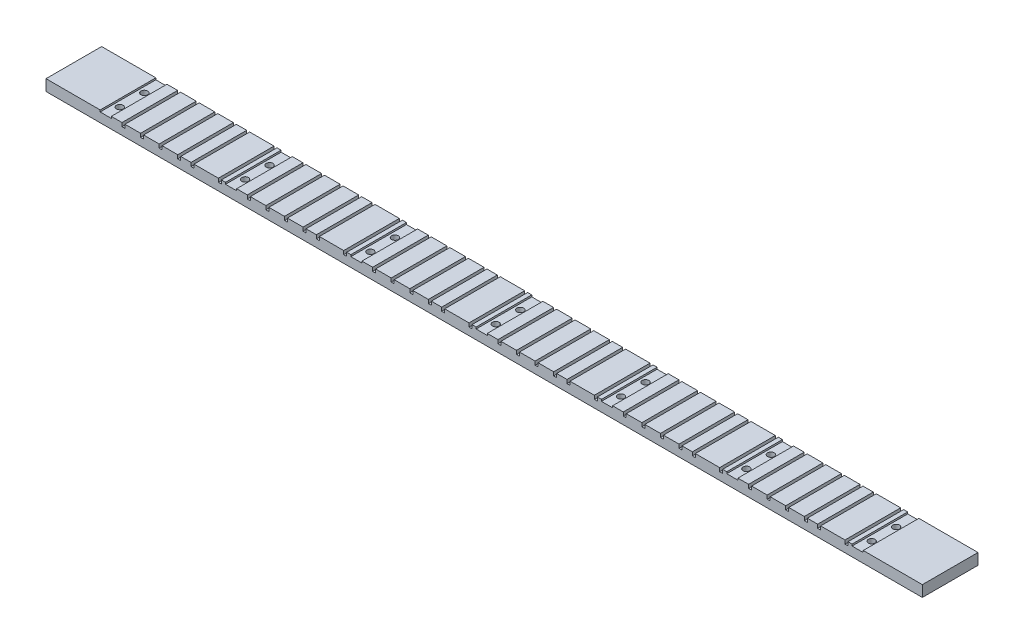
SolidWorks part; units mm, degrees
ref_plane "Front Plane" through (0, 0, 0) normal (0, 0, 1) x (1, 0, 0)
ref_plane "Top Plane" through (0, 0, 0) normal (0, 1, 0) x (1, 0, 0)
ref_plane "Right Plane" through (0, 0, 0) normal (1, 0, 0) x (0, 0, -1)
ref_plane "Plane1" through (0, 2, 0) normal (0, -1, 0) x (-1, 0, 0)
sketch "Sketch1" plane through (0, 2, 0) normal (0, -1, 0) x (-1, 0, 0)
  line L1 (100, 20) -> (-400, 20)
  line L2 (100, 20) -> (100, 51.75)
  line L3 (100, 51.75) -> (-400, 51.75)
  line L4 (-400, 20) -> (-400, 51.75)
extrude "Boss-Extrude1" add sketch "Sketch1" along normal blind 6.35
sketch "Sketch5" plane through (0, 0, -51.75) normal (0, 0, -1) x (-1, 0, 0)
  line L0 (-1.5747, 2.0001) -> (-0.0572, 2.0001)
  line L1 (-1.5747, 3.3668) -> (-1.5747, 2.0001)
  line L2 (61.7105, 3.3668) -> (-1.5747, 3.3668)
  line L3 (61.7105, 2.0001) -> (61.7105, 3.3668)
  line L4 (56.6446, -0.0571) -> (56.6446, 2.0001)
  line L5 (54.9428, 2.0001) -> (54.9428, -0.0571)
  line L6 (46.0446, 2.0001) -> (54.9428, 2.0001)
  line L7 (46.0446, -0.0571) -> (46.0446, 2.0001)
  line L8 (44.3428, -0.0571) -> (46.0446, -0.0571)
  line L9 (44.3428, 2.0001) -> (44.3428, -0.0571)
  line L10 (35.4446, 2.0001) -> (44.3428, 2.0001)
  line L11 (35.4446, -0.0571) -> (35.4446, 2.0001)
  line L12 (33.7428, -0.0571) -> (35.4446, -0.0571)
  line L174 (54.9428, -0.0571) -> (56.6446, -0.0571)
  line L181 (33.7428, 2.0001) -> (33.7428, -0.0571)
  line L182 (24.8446, 2.0001) -> (33.7428, 2.0001)
  line L183 (24.8446, -0.0571) -> (24.8446, 2.0001)
  line L184 (23.1428, -0.0571) -> (24.8446, -0.0571)
  line L185 (23.1428, 2.0001) -> (23.1428, -0.0571)
  line L186 (17.2446, 2.0001) -> (23.1428, 2.0001)
  line L187 (17.2446, -0.0571) -> (17.2446, 2.0001)
  line L188 (15.5428, -0.0571) -> (17.2446, -0.0571)
  line L189 (15.5428, 2.0001) -> (15.5428, -0.0571)
  line L190 (1.6446, 2.0001) -> (15.5428, 2.0001)
  line L191 (1.6446, -0.0571) -> (1.6446, 2.0001)
  line L192 (-0.0572, -0.0571) -> (1.6446, -0.0571)
  line L193 (-0.0572, 2.0001) -> (-0.0572, -0.0571)
  line L194 (-73.0747, 2.0001) -> (-71.5572, 2.0001)
  line L195 (-73.0747, 3.3668) -> (-73.0747, 2.0001)
  line L196 (-9.7895, 3.3668) -> (-73.0747, 3.3668)
  line L197 (-9.7895, 2.0001) -> (-9.7895, 3.3668)
  line L198 (-14.8554, 2.0001) -> (-9.7895, 2.0001)
  line L199 (-14.8554, -0.0571) -> (-14.8554, 2.0001)
  line L200 (-16.5572, -0.0571) -> (-14.8554, -0.0571)
  line L201 (-16.5572, 2.0001) -> (-16.5572, -0.0571)
  line L202 (-25.4554, 2.0001) -> (-16.5572, 2.0001)
  line L203 (-25.4554, -0.0571) -> (-25.4554, 2.0001)
  line L204 (-27.1572, -0.0571) -> (-25.4554, -0.0571)
  line L205 (-27.1572, 2.0001) -> (-27.1572, -0.0571)
  line L206 (-36.0554, 2.0001) -> (-27.1572, 2.0001)
  line L207 (-36.0554, -0.0571) -> (-36.0554, 2.0001)
  line L208 (-37.7572, -0.0571) -> (-36.0554, -0.0571)
  line L209 (-37.7572, 2.0001) -> (-37.7572, -0.0571)
  line L210 (-46.6554, 2.0001) -> (-37.7572, 2.0001)
  line L211 (-46.6554, -0.0571) -> (-46.6554, 2.0001)
  line L212 (-48.3572, -0.0571) -> (-46.6554, -0.0571)
  line L213 (-48.3572, 2.0001) -> (-48.3572, -0.0571)
  line L214 (-54.2554, 2.0001) -> (-48.3572, 2.0001)
  line L215 (-54.2554, -0.0571) -> (-54.2554, 2.0001)
  line L216 (-55.9572, -0.0571) -> (-54.2554, -0.0571)
  line L217 (-55.9572, 2.0001) -> (-55.9572, -0.0571)
  line L218 (-69.8554, 2.0001) -> (-55.9572, 2.0001)
  line L219 (-69.8554, -0.0571) -> (-69.8554, 2.0001)
  line L220 (-71.5572, -0.0571) -> (-69.8554, -0.0571)
  line L221 (-71.5572, 2.0001) -> (-71.5572, -0.0571)
  line L222 (-144.5747, 2.0001) -> (-143.0572, 2.0001)
  line L223 (-144.5747, 3.3668) -> (-144.5747, 2.0001)
  line L224 (-81.2895, 3.3668) -> (-144.5747, 3.3668)
  line L225 (-81.2895, 2.0001) -> (-81.2895, 3.3668)
  line L226 (-86.3554, 2.0001) -> (-81.2895, 2.0001)
  line L227 (-86.3554, -0.0571) -> (-86.3554, 2.0001)
  line L228 (-88.0572, -0.0571) -> (-86.3554, -0.0571)
  line L229 (-88.0572, 2.0001) -> (-88.0572, -0.0571)
  line L230 (-96.9554, 2.0001) -> (-88.0572, 2.0001)
  line L231 (-96.9554, -0.0571) -> (-96.9554, 2.0001)
  line L232 (-98.6572, -0.0571) -> (-96.9554, -0.0571)
  line L233 (-98.6572, 2.0001) -> (-98.6572, -0.0571)
  line L234 (-107.5554, 2.0001) -> (-98.6572, 2.0001)
  line L235 (-107.5554, -0.0571) -> (-107.5554, 2.0001)
  line L236 (-109.2572, -0.0571) -> (-107.5554, -0.0571)
  line L237 (-109.2572, 2.0001) -> (-109.2572, -0.0571)
  line L238 (-118.1554, 2.0001) -> (-109.2572, 2.0001)
  line L239 (-118.1554, -0.0571) -> (-118.1554, 2.0001)
  line L240 (-119.8572, -0.0571) -> (-118.1554, -0.0571)
  line L241 (-119.8572, 2.0001) -> (-119.8572, -0.0571)
  line L242 (-125.7554, 2.0001) -> (-119.8572, 2.0001)
  line L243 (-125.7554, -0.0571) -> (-125.7554, 2.0001)
  line L244 (-127.4572, -0.0571) -> (-125.7554, -0.0571)
  line L245 (-127.4572, 2.0001) -> (-127.4572, -0.0571)
  line L246 (-141.3554, 2.0001) -> (-127.4572, 2.0001)
  line L247 (-141.3554, -0.0571) -> (-141.3554, 2.0001)
  line L248 (-143.0572, -0.0571) -> (-141.3554, -0.0571)
  line L249 (-143.0572, 2.0001) -> (-143.0572, -0.0571)
  line L250 (-216.0747, 2.0001) -> (-214.5572, 2.0001)
  line L251 (-216.0747, 3.3668) -> (-216.0747, 2.0001)
  line L252 (-152.7895, 3.3668) -> (-216.0747, 3.3668)
  line L253 (-152.7895, 2.0001) -> (-152.7895, 3.3668)
  line L254 (-157.8554, 2.0001) -> (-152.7895, 2.0001)
  line L255 (-157.8554, -0.0571) -> (-157.8554, 2.0001)
  line L256 (-159.5572, -0.0571) -> (-157.8554, -0.0571)
  line L257 (-159.5572, 2.0001) -> (-159.5572, -0.0571)
  line L258 (-168.4554, 2.0001) -> (-159.5572, 2.0001)
  line L259 (-168.4554, -0.0571) -> (-168.4554, 2.0001)
  line L260 (-170.1572, -0.0571) -> (-168.4554, -0.0571)
  line L261 (-170.1572, 2.0001) -> (-170.1572, -0.0571)
  line L262 (-179.0554, 2.0001) -> (-170.1572, 2.0001)
  line L263 (-179.0554, -0.0571) -> (-179.0554, 2.0001)
  line L264 (-180.7572, -0.0571) -> (-179.0554, -0.0571)
  line L265 (-180.7572, 2.0001) -> (-180.7572, -0.0571)
  line L266 (-189.6554, 2.0001) -> (-180.7572, 2.0001)
  line L267 (-189.6554, -0.0571) -> (-189.6554, 2.0001)
  line L268 (-191.3572, -0.0571) -> (-189.6554, -0.0571)
  line L269 (-191.3572, 2.0001) -> (-191.3572, -0.0571)
  line L270 (-197.2554, 2.0001) -> (-191.3572, 2.0001)
  line L271 (-197.2554, -0.0571) -> (-197.2554, 2.0001)
  line L272 (-198.9572, -0.0571) -> (-197.2554, -0.0571)
  line L273 (-198.9572, 2.0001) -> (-198.9572, -0.0571)
  line L274 (-212.8554, 2.0001) -> (-198.9572, 2.0001)
  line L275 (-212.8554, -0.0571) -> (-212.8554, 2.0001)
  line L276 (-214.5572, -0.0571) -> (-212.8554, -0.0571)
  line L277 (-214.5572, 2.0001) -> (-214.5572, -0.0571)
  line L278 (-287.5747, 2.0001) -> (-286.0572, 2.0001)
  line L279 (-287.5747, 3.3668) -> (-287.5747, 2.0001)
  line L280 (-224.2895, 3.3668) -> (-287.5747, 3.3668)
  line L281 (-224.2895, 2.0001) -> (-224.2895, 3.3668)
  line L282 (-229.3554, 2.0001) -> (-224.2895, 2.0001)
  line L283 (-229.3554, -0.0571) -> (-229.3554, 2.0001)
  line L284 (-231.0572, -0.0571) -> (-229.3554, -0.0571)
  line L285 (-231.0572, 2.0001) -> (-231.0572, -0.0571)
  line L286 (-239.9554, 2.0001) -> (-231.0572, 2.0001)
  line L287 (-239.9554, -0.0571) -> (-239.9554, 2.0001)
  line L288 (-241.6572, -0.0571) -> (-239.9554, -0.0571)
  line L289 (-241.6572, 2.0001) -> (-241.6572, -0.0571)
  line L290 (-250.5554, 2.0001) -> (-241.6572, 2.0001)
  line L291 (-250.5554, -0.0571) -> (-250.5554, 2.0001)
  line L292 (-252.2572, -0.0571) -> (-250.5554, -0.0571)
  line L293 (-252.2572, 2.0001) -> (-252.2572, -0.0571)
  line L294 (-261.1554, 2.0001) -> (-252.2572, 2.0001)
  line L295 (-261.1554, -0.0571) -> (-261.1554, 2.0001)
  line L296 (-262.8572, -0.0571) -> (-261.1554, -0.0571)
  line L297 (-262.8572, 2.0001) -> (-262.8572, -0.0571)
  line L298 (-268.7554, 2.0001) -> (-262.8572, 2.0001)
  line L299 (-268.7554, -0.0571) -> (-268.7554, 2.0001)
  line L300 (-270.4572, -0.0571) -> (-268.7554, -0.0571)
  line L301 (-270.4572, 2.0001) -> (-270.4572, -0.0571)
  line L302 (-284.3554, 2.0001) -> (-270.4572, 2.0001)
  line L303 (-284.3554, -0.0571) -> (-284.3554, 2.0001)
  line L304 (-286.0572, -0.0571) -> (-284.3554, -0.0571)
  line L305 (-286.0572, 2.0001) -> (-286.0572, -0.0571)
  line L306 (-359.0747, 2.0001) -> (-357.5572, 2.0001)
  line L307 (-359.0747, 3.3668) -> (-359.0747, 2.0001)
  line L308 (-295.7895, 3.3668) -> (-359.0747, 3.3668)
  line L309 (-295.7895, 2.0001) -> (-295.7895, 3.3668)
  line L310 (-300.8554, 2.0001) -> (-295.7895, 2.0001)
  line L311 (-300.8554, -0.0571) -> (-300.8554, 2.0001)
  line L312 (-302.5572, -0.0571) -> (-300.8554, -0.0571)
  line L313 (-302.5572, 2.0001) -> (-302.5572, -0.0571)
  line L314 (-311.4554, 2.0001) -> (-302.5572, 2.0001)
  line L315 (-311.4554, -0.0571) -> (-311.4554, 2.0001)
  line L316 (-313.1572, -0.0571) -> (-311.4554, -0.0571)
  line L317 (-313.1572, 2.0001) -> (-313.1572, -0.0571)
  line L318 (-322.0554, 2.0001) -> (-313.1572, 2.0001)
  line L319 (-322.0554, -0.0571) -> (-322.0554, 2.0001)
  line L320 (-323.7572, -0.0571) -> (-322.0554, -0.0571)
  line L321 (-323.7572, 2.0001) -> (-323.7572, -0.0571)
  line L322 (-332.6554, 2.0001) -> (-323.7572, 2.0001)
  line L323 (-332.6554, -0.0571) -> (-332.6554, 2.0001)
  line L324 (-334.3572, -0.0571) -> (-332.6554, -0.0571)
  line L325 (-334.3572, 2.0001) -> (-334.3572, -0.0571)
  line L326 (-340.2554, 2.0001) -> (-334.3572, 2.0001)
  line L327 (-340.2554, -0.0571) -> (-340.2554, 2.0001)
  line L328 (-341.9572, -0.0571) -> (-340.2554, -0.0571)
  line L329 (-341.9572, 2.0001) -> (-341.9572, -0.0571)
  line L330 (-355.8554, 2.0001) -> (-341.9572, 2.0001)
  line L331 (-355.8554, -0.0571) -> (-355.8554, 2.0001)
  line L332 (-357.5572, -0.0571) -> (-355.8554, -0.0571)
  line L333 (-357.5572, 2.0001) -> (-357.5572, -0.0571)
  line L334 (56.6446, 2.0001) -> (61.7105, 2.0001)
extrude "Cut-Extrude2" cut sketch "Sketch5" against normal through all
sketch "Sketch7" plane through (0, 0, -20) normal (0, 0, 1) x (1, 0, 0)
  line L0 (-71.12, 3.6453) -> (-71.12, 2)
  line L2 (-71.12, 2) -> (-69.0919, 2)
  line L3 (-69.0919, 2) -> (-69.0919, 1)
  line L4 (-69.0919, 1) -> (-62.7419, 1)
  line L5 (-62.7419, 1) -> (-62.7419, 2)
  line L6 (-62.7419, 2) -> (-60.964, 2)
  line L7 (-60.964, 2) -> (-60.964, 3.6453)
  line L8 (-71.12, 3.6453) -> (-60.964, 3.6453)
  line L9 (0.38, 3.6453) -> (0.38, 2)
  line L10 (0.38, 2) -> (2.4081, 2)
  line L11 (2.4081, 2) -> (2.4081, 1)
  line L12 (2.4081, 1) -> (8.7581, 1)
  line L13 (8.7581, 1) -> (8.7581, 2)
  line L14 (8.7581, 2) -> (10.536, 2)
  line L15 (10.536, 2) -> (10.536, 3.6453)
  line L16 (0.38, 3.6453) -> (10.536, 3.6453)
  line L17 (71.88, 3.6453) -> (71.88, 2)
  line L18 (71.88, 2) -> (73.9081, 2)
  line L19 (73.9081, 2) -> (73.9081, 1)
  line L20 (73.9081, 1) -> (80.2581, 1)
  line L21 (80.2581, 1) -> (80.2581, 2)
  line L22 (80.2581, 2) -> (82.036, 2)
  line L23 (82.036, 2) -> (82.036, 3.6453)
  line L24 (71.88, 3.6453) -> (82.036, 3.6453)
  line L25 (143.38, 3.6453) -> (143.38, 2)
  line L26 (143.38, 2) -> (145.4081, 2)
  line L27 (145.4081, 2) -> (145.4081, 1)
  line L28 (145.4081, 1) -> (151.7581, 1)
  line L29 (151.7581, 1) -> (151.7581, 2)
  line L30 (151.7581, 2) -> (153.536, 2)
  line L31 (153.536, 2) -> (153.536, 3.6453)
  line L32 (143.38, 3.6453) -> (153.536, 3.6453)
  line L33 (214.88, 3.6453) -> (214.88, 2)
  line L34 (214.88, 2) -> (216.9081, 2)
  line L35 (216.9081, 2) -> (216.9081, 1)
  line L36 (216.9081, 1) -> (223.2581, 1)
  line L37 (223.2581, 1) -> (223.2581, 2)
  line L38 (223.2581, 2) -> (225.036, 2)
  line L39 (225.036, 2) -> (225.036, 3.6453)
  line L40 (214.88, 3.6453) -> (225.036, 3.6453)
  line L41 (286.38, 3.6453) -> (286.38, 2)
  line L42 (286.38, 2) -> (288.4081, 2)
  line L43 (288.4081, 2) -> (288.4081, 1)
  line L44 (288.4081, 1) -> (294.7581, 1)
  line L45 (294.7581, 1) -> (294.7581, 2)
  line L46 (294.7581, 2) -> (296.536, 2)
  line L47 (296.536, 2) -> (296.536, 3.6453)
  line L48 (286.38, 3.6453) -> (296.536, 3.6453)
  line L49 (357.88, 3.6453) -> (357.88, 2)
  line L50 (357.88, 2) -> (359.9081, 2)
  line L51 (359.9081, 2) -> (359.9081, 1)
  line L52 (359.9081, 1) -> (366.2581, 1)
  line L53 (366.2581, 1) -> (366.2581, 2)
  line L54 (366.2581, 2) -> (368.036, 2)
  line L55 (368.036, 2) -> (368.036, 3.6453)
  line L56 (357.88, 3.6453) -> (368.036, 3.6453)
  dimension "D1" = 7
extrude "Cut-Extrude4" cut sketch "Sketch7" against normal through all
sketch "Sketch6" plane through (0, 1, 0) normal (0, -1, 0) x (1, 0, 0)
  line L0 (-65.9169, -20) -> (-65.9169, -49.7477) construction
  line L1 (400, -20) -> (-100, -20) construction
  line L2 (-65.9169, -24.3797) -> (-62.7419, -24.3797) construction
  line L3 (-65.9169, -47.1776) -> (-69.0919, -47.1776) construction
  line L4 (-62.7419, -51.75) -> (-62.7419, -20) construction
  line L5 (-69.0919, -51.75) -> (-69.0919, -20) construction
  circle A0 centre (-65.9169, -42) radius 1.8987
  circle A1 centre (-65.9169, -28) radius 1.8987
  circle A5 centre (5.5831, -42) radius 1.8987
  circle A6 centre (5.5831, -28) radius 1.8987
  circle A7 centre (77.0831, -42) radius 1.8987
  circle A8 centre (77.0831, -28) radius 1.8987
  circle A9 centre (148.5831, -42) radius 1.8987
  circle A10 centre (148.5831, -28) radius 1.8987
  circle A11 centre (220.0831, -42) radius 1.8987
  circle A12 centre (220.0831, -28) radius 1.8987
  circle A13 centre (291.5831, -42) radius 1.8987
  circle A14 centre (291.5831, -28) radius 1.8987
  circle A15 centre (363.0831, -42) radius 1.8987
  circle A16 centre (363.0831, -28) radius 1.8987
  dimension "D1" = 7
extrude "Cut-Extrude3" cut sketch "Sketch6" along normal through all
